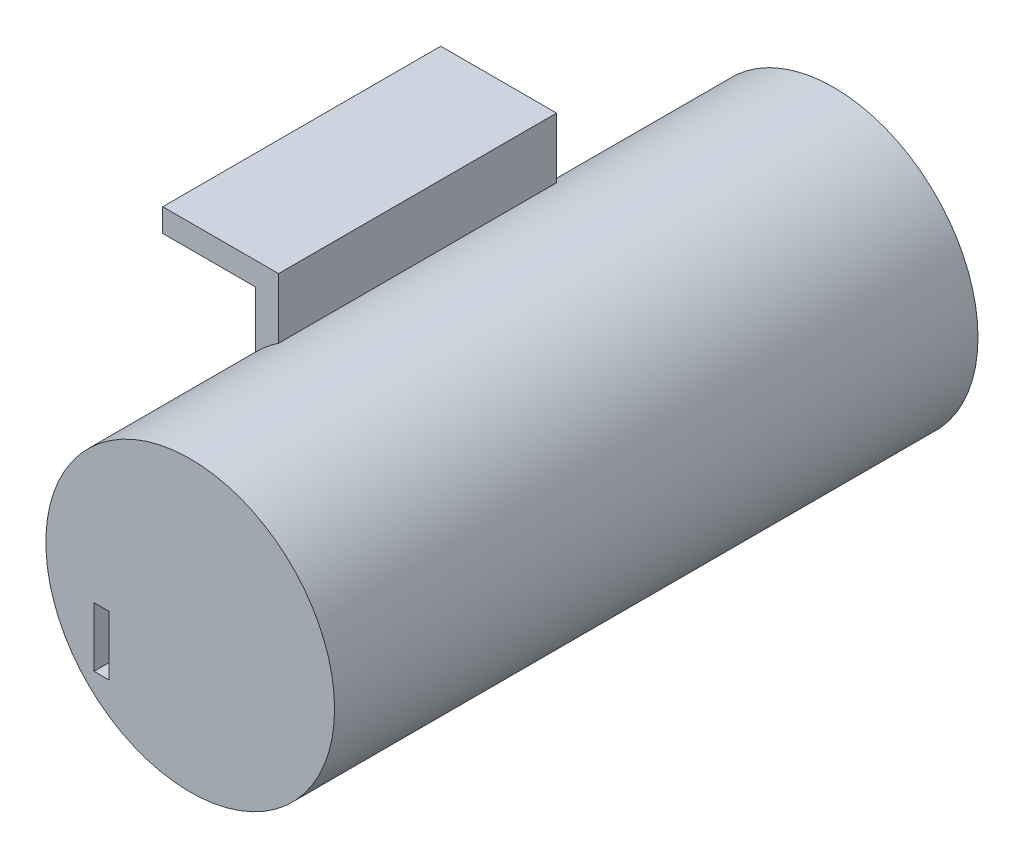
SolidWorks part; units mm, degrees
ref_plane "Front" through (0, 0, 0) normal (0, 0, 1) x (1, 0, 0)
ref_plane "Top" through (0, 0, 0) normal (0, 1, 0) x (1, 0, 0)
ref_plane "Right" through (0, 0, 0) normal (1, 0, 0) x (0, 0, -1)
sketch "Sketch1" plane through (0, 0, 0) normal (0, 0, 1) x (1, 0, 0)
  line L1 (-9.812, 11.8757) -> (-6.637, 11.8757)
  line L2 (-9.812, 11.8757) -> (-9.812, 0.8757)
  line L3 (-9.812, 0.8757) -> (-6.637, 0.8757)
  line L4 (-6.637, 11.8757) -> (-6.637, 0.8757)
  line L5 (-9.812, 8.7007) -> (-22.512, 8.7007)
  line L6 (-9.812, 8.7007) -> (-9.812, 11.8757)
  line L7 (-9.812, 11.8757) -> (-22.512, 11.8757)
  line L8 (-22.512, 8.7007) -> (-22.512, 11.8757)
  dimension "D1" = 11
  dimension "D2" = 3.175
  dimension "D3" = 3.175
  dimension "D4" = 12.7
extrude "Boss-Extrude1" add sketch "Sketch1" along normal blind 38.1 contours L8 L5 L2 L7 | L4 L1 L2 L3
sketch "Sketch2" plane through (0, 0, 0) normal (0, 0, -1) x (-1, 0, 0)
  circle A0 centre (-4.3298, -12.862) radius 19.7846
  circle A1 centre (-4.3298, -12.862) radius 18.4
extrude "Boss-Extrude2" add sketch "Sketch2" against normal blind 58 and the other way blind 27
sketch "Sketch3" plane through (0, 0, 58) normal (0, 0, 1) x (1, 0, 0)
  circle A0 centre (4.3298, -12.862) radius 19.7846
extrude "Boss-Extrude3" add sketch "Sketch3" along normal blind 3.175
sketch "Sketch4" plane through (0, 0, 61.175) normal (0, 0, 1) x (1, 0, 0)
  line L1 (-8.8496, -16.7508) -> (-6.7962, -16.7508)
  line L2 (-8.8496, -16.7508) -> (-8.8496, -24.8958)
  line L3 (-8.8496, -24.8958) -> (-6.7962, -24.8958)
  line L4 (-6.7962, -16.7508) -> (-6.7962, -24.8958)
extrude "Cut-Extrude1" cut sketch "Sketch4" against normal blind 3.175
